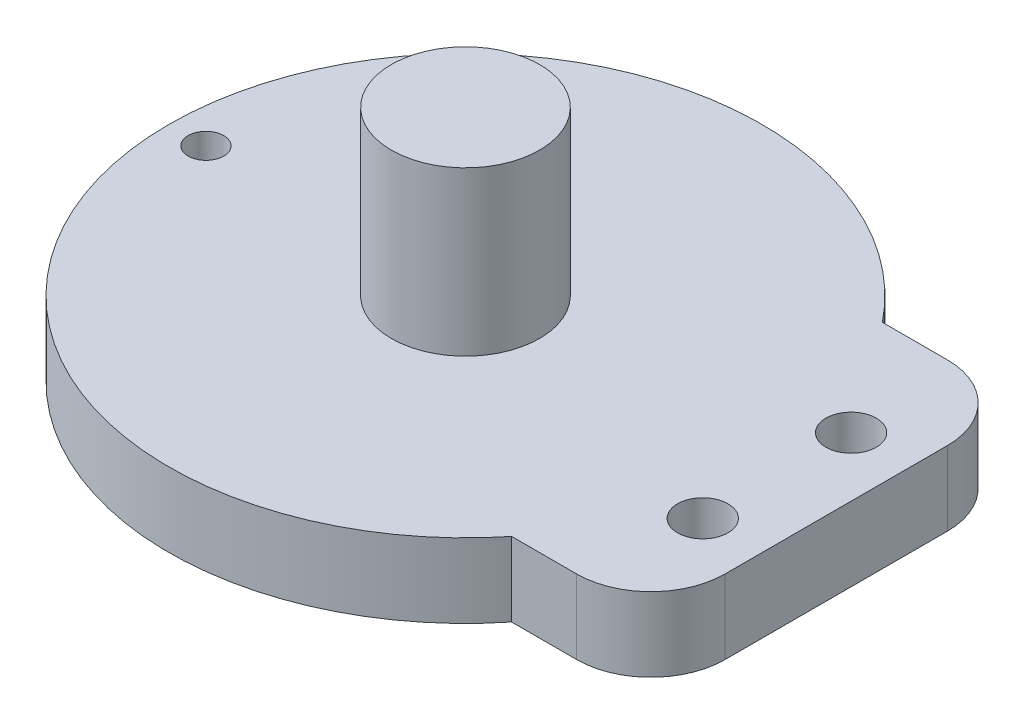
SolidWorks part; units mm, degrees
ref_plane "정면" through (0, 0, 0) normal (0, 0, 1) x (1, 0, 0)
ref_plane "윗면" through (0, 0, 0) normal (0, 1, 0) x (1, 0, 0)
ref_plane "우측면" through (0, 0, 0) normal (1, 0, 0) x (0, 0, -1)
sketch "스케치1" plane through (0, 0, 0) normal (0, 1, 0) x (1, 0, 0)
  line L1 (15.6125, 12.5) -> (25, 12.5)
  line L3 (15.6125, -12.5) -> (25, -12.5)
  line L4 (25, 12.5) -> (25, -12.5)
  arc A0 (15.6125, 12.5) -> (15.6125, -12.5) centre (0, 0) ccw
  dimension "D1" = 40
  dimension "D3" = 25
extrude "보스-돌출1" add sketch "스케치1" along normal blind 5
sketch "스케치2" plane through (0, 5, 0) normal (0, 1, 0) x (1, 0, 0)
  circle A0 centre (0, 0) radius 5
  dimension "D1" = 10
extrude "보스-돌출2" add sketch "스케치2" along normal blind 11
sketch "스케치3" plane through (0, 5, 0) normal (0, 1, 0) x (1, 0, 0)
  line L0 (0, 0) -> (50000, 0) construction
  line L1 (0, 0) -> (38302.2222, 32139.3805) construction
  line L2 (0, 0) -> (38302.2222, -32139.3805) construction
  line L3 (21, 0) -> (21, 50000) construction
  line L5 (0, 0) -> (0, 50000) construction
  circle A0 centre (-17.5, 0) radius 1.2
  circle A1 centre (0, 0) radius 17.5 construction
  circle A2 centre (21, 5) radius 1.7
  circle A3 centre (21, -5) radius 1.7
  dimension "D1" = 2.4
  dimension "D4" = 35
  dimension "D5" = 3.4
  dimension "D6" = 3.4
  dimension "D2" = 40
  dimension "D3" = 40
  dimension "D7" = 5
  dimension "D8" = 5
  dimension "D9" = 21
extrude "컷-돌출1" cut sketch "스케치3" against normal up to next
sketch "스케치4" plane through (0, 0, 0) normal (0, -1, 0) x (1, 0, 0)
  circle A0 centre (-17.5, 0) radius 2
  circle A1 centre (21, 5) radius 3
  circle A2 centre (21, -5) radius 3
  dimension "D1" = 4
  dimension "D2" = 6
  dimension "D3" = 6
extrude "컷-돌출2" cut sketch "스케치4" against normal blind 2
fillet "필렛1" radius 5 2 edges at (25, 2.5, 12.5) (25, 2.5, -12.5)
